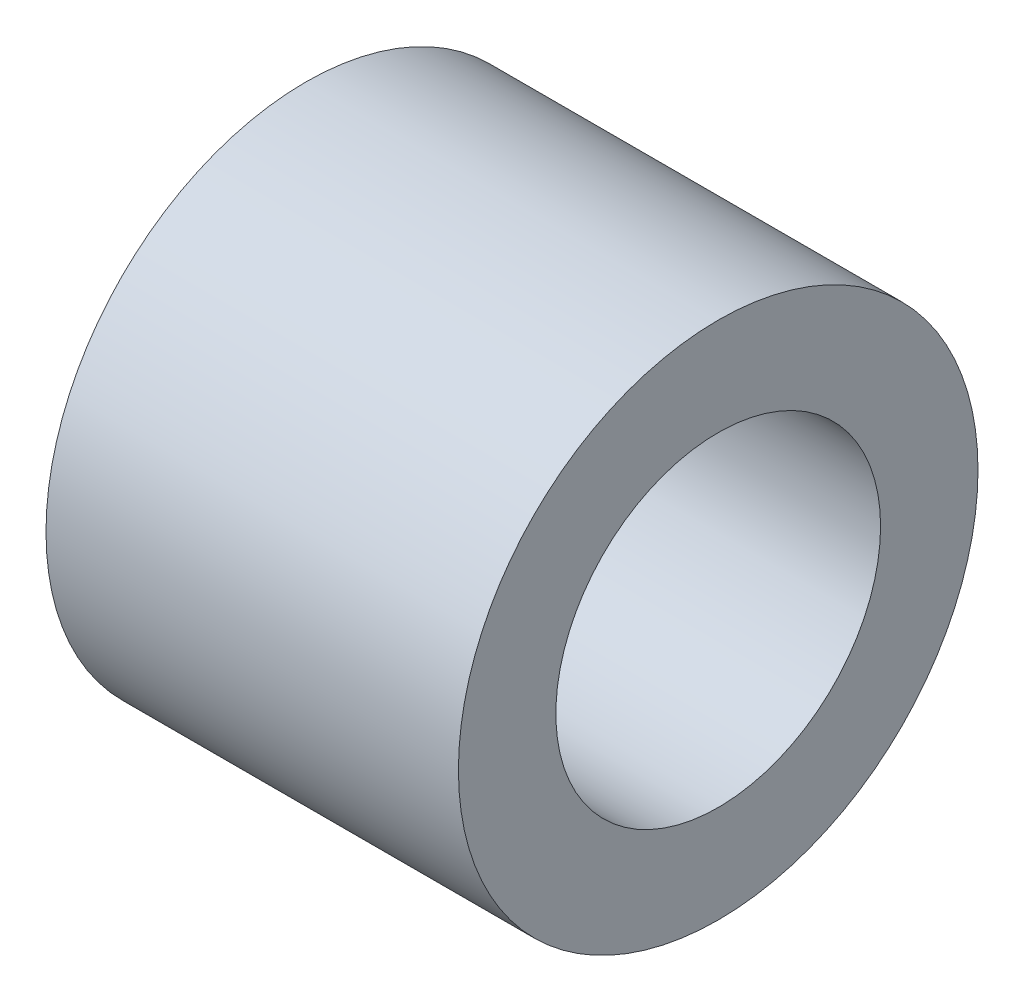
SolidWorks part; units mm, degrees
material "Chrome Stainless Steel"
ref_plane "Front Plane" through (0, 0, 0) normal (0, 0, 1) x (1, 0, 0)
ref_plane "Top Plane" through (0, 0, 0) normal (0, 1, 0) x (1, 0, 0)
ref_plane "Right Plane" through (0, 0, 0) normal (1, 0, 0) x (0, 0, -1)
sketch "Sketch1" plane through (0, 0, 0) normal (0, 0, 1) x (1, 0, 0)
  line L0 (-3.175, 2.5) -> (3.175, 2.5)
  line L1 (0, 2.5) -> (0, 0) construction
  line L2 (3.175, 2.5) -> (3.175, 4)
  line L3 (3.175, 4) -> (-3.175, 4)
  line L4 (-3.175, 4) -> (-3.175, 2.5)
  line L5 (0, 0) -> (-8.5488, 0) construction
  dimension "D1" = 2.5
  dimension "D2" = 6.35
  dimension "D3" = 1.5
revolve "Revolve1" add sketch "Sketch1" angle 360 about L5
